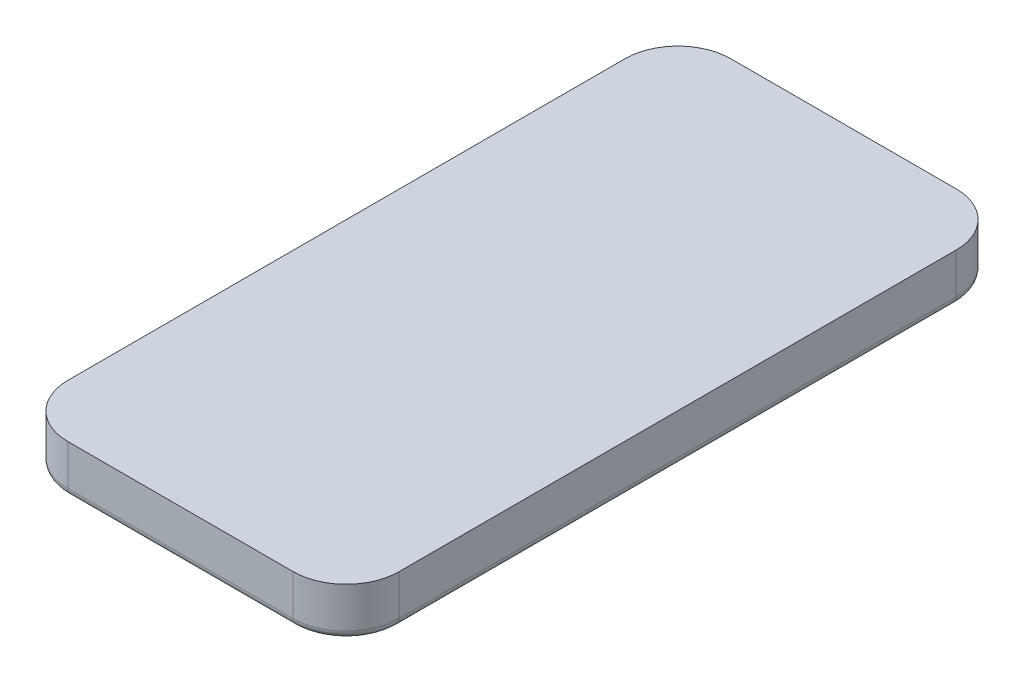
SolidWorks part; units mm, degrees
ref_plane "前视基准面" through (0, 0, 0) normal (0, 0, 1) x (1, 0, 0)
ref_plane "上视基准面" through (0, 0, 0) normal (0, 1, 0) x (1, 0, 0)
ref_plane "右视基准面" through (0, 0, 0) normal (1, 0, 0) x (0, 0, -1)
sketch "草图1" plane through (0, 0, 0) normal (0, 1, 0) x (1, 0, 0)
  line L0 (0, -75.15) -> (0, 75.15) construction
  line L1 (-37.55, 75.15) -> (37.55, 75.15)
  line L2 (37.55, 75.15) -> (37.55, -75.15)
  line L3 (37.55, -75.15) -> (-37.55, -75.15)
  line L4 (-37.55, -75.15) -> (-37.55, 75.15)
  point P4 (0, 0)
  point P8 (0, 75.15)
  dimension "D1" = 75.1
  dimension "D2" = 150.3
extrude "凸台-拉伸1" add sketch "草图1" along normal blind 11
fillet "圆角1" radius 12 4 edges at (37.55, 5.5, -75.15) (37.55, 5.5, 75.15) (-37.55, 5.5, 75.15) (-37.55, 5.5, -75.15)
fillet "圆角2" radius 1.8 8 edges at (0, 0, -75.15) (-34.0353, 0, -71.6353) (-37.55, 0, 0) (-34.0353, 0, 71.6353) (0, 0, 75.15) (34.0353, 0, 71.6353) (37.55, 0, 0) (34.0353, 0, -71.6353)
sketch "草图2" plane through (0, 0, 0) normal (0, -1, 0) x (1, 0, 0)
  line L0 (-25.55, 75.15) -> (25.55, 75.15) construction
  line L1 (-25.55, 75.15) -> (25.55, 75.15) construction
  line L2 (21.45, -29.85) -> (5.45, -29.85)
  line L3 (-6.55, -41.85) -> (-6.55, -58.65)
  line L4 (5.45, -70.65) -> (21.45, -70.65)
  line L5 (33.45, -58.65) -> (33.45, -41.85)
  line L6 (-37.55, -63.15) -> (-37.55, 63.15) construction
  arc A0 (33.45, -58.65) -> (21.45, -70.65) centre (21.45, -58.65) cw
  arc A1 (-6.55, -58.65) -> (5.45, -70.65) centre (5.45, -58.65) ccw
  arc A2 (5.45, -29.85) -> (-6.55, -41.85) centre (5.45, -41.85) ccw
  arc A3 (21.45, -29.85) -> (33.45, -41.85) centre (21.45, -41.85) cw
  point P10 (33.45, -70.65)
  point P13 (-6.55, -70.65)
  point P16 (-6.55, -29.85)
  dimension "D5" = 12
  dimension "D1" = 40
  dimension "D2" = 40.8
  dimension "D3" = 105
  dimension "D4" = 31
extrude "凸台-拉伸2" add sketch "草图2" along normal blind 2.5
sketch "草图3" plane through (0, -2.5, 0) normal (0, -1, 0) x (1, 0, 0)
  line L0 (0, -73.35) -> (0, 73.35) construction
  line L1 (25.55, 73.35) -> (-25.55, 73.35) construction
  line L2 (-25.55, -73.35) -> (25.55, -73.35) construction
  circle A0 centre (0, 0) radius 30 construction
  dimension "D1" = 60
